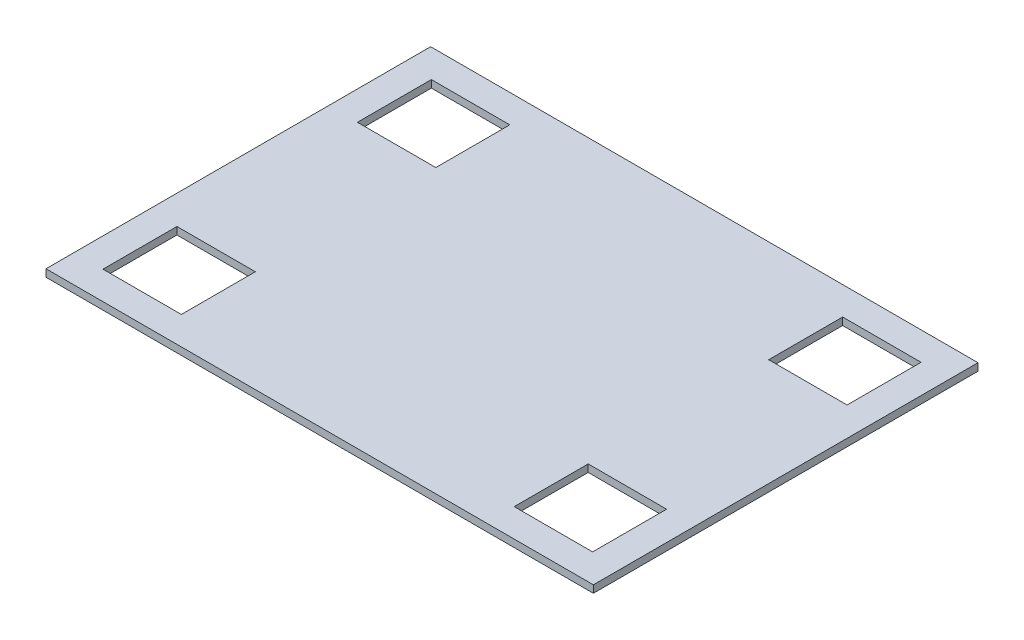
SolidWorks part; units mm, degrees
ref_plane "Front Plane" through (0, 0, 0) normal (0, 0, 1) x (1, 0, 0)
ref_plane "Top Plane" through (0, 0, 0) normal (0, 1, 0) x (1, 0, 0)
ref_plane "Right Plane" through (0, 0, 0) normal (1, 0, 0) x (0, 0, -1)
sketch "Sketch1" plane through (0, 0, 0) normal (0, 1, 0) x (1, 0, 0)
  line L1 (-185, 130) -> (185, 130)
  line L2 (-185, 130) -> (-185, -130)
  line L3 (-185, -130) -> (185, -130)
  line L4 (185, 130) -> (185, -130)
  line L5 (-185, 130) -> (185, -130) construction
  line L6 (-185, -130) -> (185, 130) construction
  point P0 (0, 0)
  dimension "D1" = 370
  dimension "D2" = 260
extrude "Boss-Extrude1" add sketch "Sketch1" along normal blind 5
sketch "Sketch3" plane through (0, 0, 0) normal (0, -1, 0) x (1, 0, 0)
  line L5 (185, 130) -> (185, -130) construction
  line L7 (185, -61) -> (185, 61)
  line L8 (112.5, 61) -> (165.5, 61)
  line L25 (-112.5, 61) -> (-112.5, 111)
  line L26 (-112.5, 111) -> (-165.5, 111)
  line L27 (-112.5, 61) -> (-165.5, 61)
  line L28 (-165.5, 111) -> (-165.5, 61)
  line L29 (165.5, 111) -> (165.5, 61)
  line L30 (112.5, 111) -> (165.5, 111)
  line L31 (112.5, 61) -> (112.5, 111)
  line L32 (112.5, -61) -> (112.5, -111)
  line L34 (112.5, -111) -> (165.5, -111)
  line L35 (165.5, -111) -> (165.5, -61)
  line L36 (112.5, -61) -> (165.5, -61)
  line L37 (-112.5, -61) -> (-165.5, -61)
  line L38 (-165.5, -111) -> (-165.5, -61)
  line L39 (-112.5, -111) -> (-165.5, -111)
  line L40 (-112.5, -61) -> (-112.5, -111)
  dimension "D1" = 53
extrude "Cut-Extrude3" cut sketch "Sketch3" against normal blind 10 contours L26 L28 L27 L25 | L40 L37 L38 L39 | L31 L8 L29 L30 | L36 L32 L34 L35
